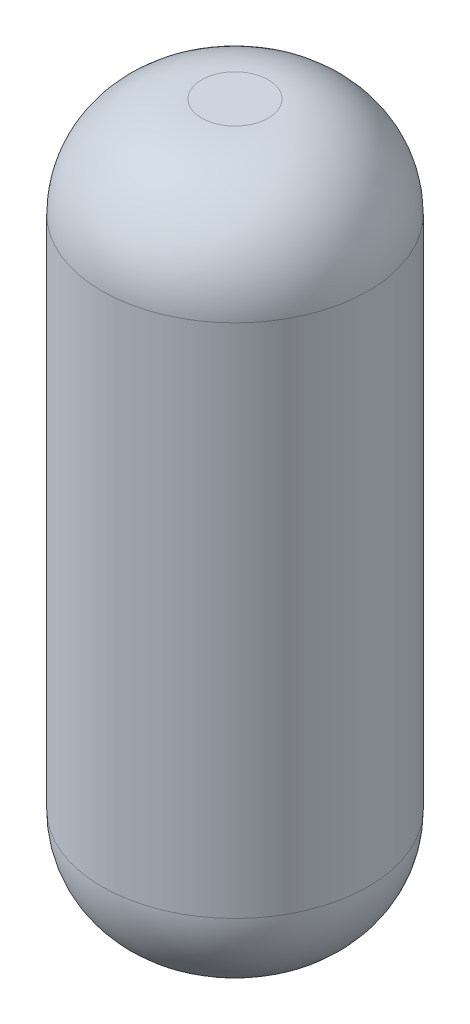
SolidWorks part; units mm, degrees
ref_plane "Alzado" through (0, 0, 0) normal (0, 0, 1) x (1, 0, 0)
ref_plane "Planta" through (0, 0, 0) normal (0, 1, 0) x (1, 0, 0)
ref_plane "Vista lateral" through (0, 0, 0) normal (1, 0, 0) x (0, 0, -1)
sketch "Croquis1" plane through (0, 0, 0) normal (0, 1, 0) x (1, 0, 0)
  circle A0 centre (0, 0) radius 4
  dimension "D1" = 8
extrude "Saliente-Extruir1" add sketch "Croquis1" along normal blind 21.5
fillet "Redondeo1" radius 3 2 edges at (0, 0, 4) (0, 21.5, 4)
